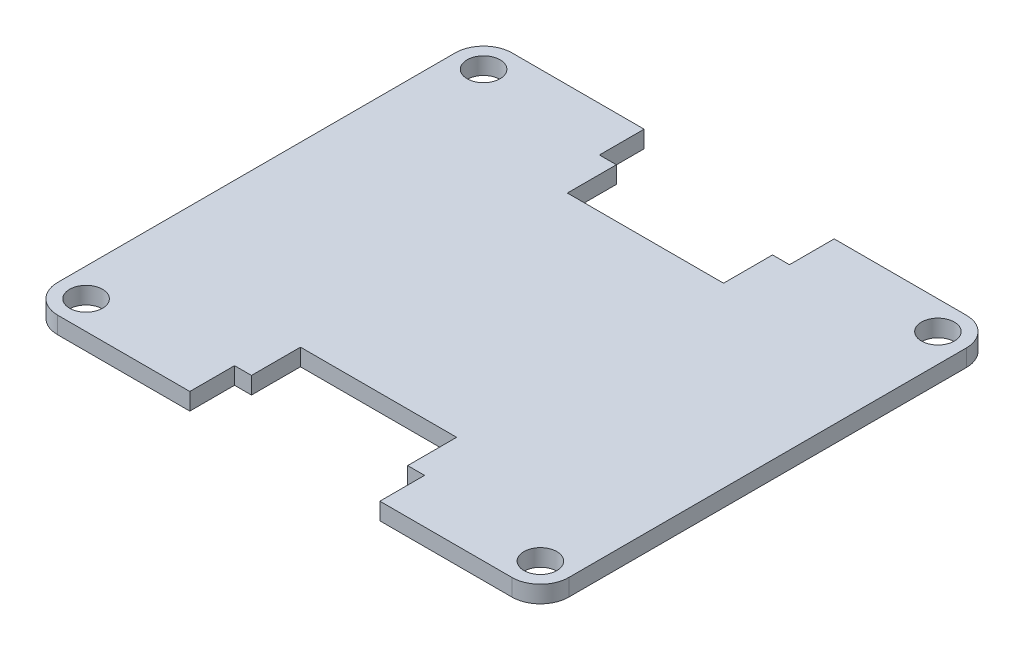
SolidWorks part; units mm, degrees
ref_plane "Front Plane" through (0, 0, 0) normal (0, 0, 1) x (1, 0, 0)
ref_plane "Top Plane" through (0, 0, 0) normal (0, 1, 0) x (1, 0, 0)
ref_plane "Right Plane" through (0, 0, 0) normal (1, 0, 0) x (0, 0, -1)
sketch "Sketch1" plane through (0, 0, 0) normal (0, 1, 0) x (1, 0, 0)
  line L1 (-22.86, 20.32) -> (22.86, 20.32)
  line L2 (-22.86, 20.32) -> (-22.86, -20.32)
  line L3 (-22.86, -20.32) -> (22.86, -20.32)
  line L4 (22.86, 20.32) -> (22.86, -20.32)
  line L5 (-22.86, 20.32) -> (22.86, -20.32) construction
  line L6 (-22.86, -20.32) -> (22.86, 20.32) construction
  point P0 (0, 0)
  dimension "D1" = 40.64
  dimension "D2" = 45.72
extrude "Boss-Extrude1" add sketch "Sketch1" along normal mid plane 1.524
fillet "Fillet1" radius 2.54 4 edges at (22.86, 0, -20.32) (-22.86, 0, -20.32) (22.86, 0, 20.32) (-22.86, 0, 20.32)
hole_wizard "#4 Clearance Hole1" positions "Sketch2" profile "Sketch3" hole size "#4" standard "ANSI Inch" end condition through all
sketch "Sketch2" plane through (0, 0.762, 0) normal (0, 1, 0) x (1, 0, 0)
  line L1 (-20.32, -17.78) -> (20.32, -17.78)
  line L2 (-20.32, -17.78) -> (-20.32, 17.78)
  line L3 (-20.32, 17.78) -> (20.32, 17.78)
  line L4 (20.32, -17.78) -> (20.32, 17.78)
  line L5 (-20.32, -17.78) -> (20.32, 17.78) construction
  line L6 (-20.32, 17.78) -> (20.32, -17.78) construction
  point P2 (20.32, 17.78)
  point P63 (-20.32, -17.78)
  point P64 (-20.32, 17.78)
  point P65 (20.32, -17.78)
  dimension "D1" = 35.56
  dimension "D2" = 40.64
sketch "Sketch3" plane through (20.32, 0.762, -17.78) normal (1, 0, 0) x (0, 0, 1)
  line L0 (0, 0) -> (0, 1.524)
  line L1 (0, 1.524) -> (1.4732, 1.524)
  line L2 (1.4732, 1.524) -> (1.4732, 0)
  line L5 (1.4732, 0) -> (0, 0)
  line L11 (0, -6.35) -> (0, 107.95) construction
  dimension "Thru Hole Dia." = 2.9464
  dimension "Thru Hole Depth" = 1.524
sketch "Sketch4" plane through (0, 0.762, 0) normal (0, 1, 0) x (1, 0, 0)
  line L0 (20.32, 20.32) -> (-20.32, 20.32) construction
  line L1 (6.985, 20.32) -> (-6.985, 20.32)
  line L2 (6.985, 20.32) -> (6.985, 11.938)
  line L3 (6.985, 11.938) -> (-6.985, 11.938)
  line L4 (-6.985, 20.32) -> (-6.985, 11.938)
  line L5 (0, 20.32) -> (0, 0) construction
  line L6 (6.985, 16.32) -> (8.5, 16.32)
  line L7 (8.5, 16.32) -> (8.5, 20.32)
  line L8 (8.5, 20.32) -> (6.985, 20.32)
  line L10 (-6.985, 20.32) -> (-8.5, 20.32)
  line L11 (-6.985, 20.32) -> (-6.985, 16.32)
  line L12 (-6.985, 16.32) -> (-8.5, 16.32)
  line L13 (-8.5, 20.32) -> (-8.5, 16.32)
  line M11 (20.32, 20.32) -> (-20.32, 20.32)
  dimension "D1" = 6.985
  dimension "D2" = 8.382
  dimension "D3" = 8.5
  dimension "D4" = 4
extrude "Cut-Extrude1" cut sketch "Sketch4" against normal through all contours L5 L1 L4 L3 | L5 L3 L2 M11 | L6 L7 L2 M11 | L13 L12 L4 M11
mirror "Mirror1" about plane through (0, 0, 0) normal (0, 0, 1) of "Cut-Extrude1"
